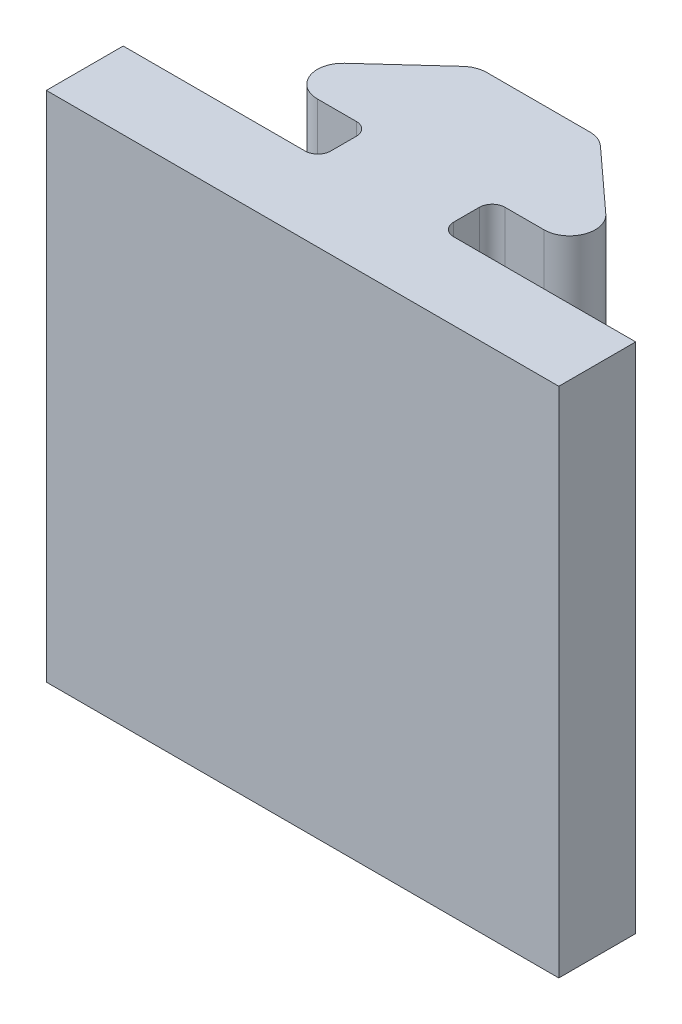
SolidWorks part; units mm, degrees
ref_plane "Front Plane" through (0, 0, 0) normal (0, 0, 1) x (1, 0, 0)
ref_plane "Top Plane" through (0, 0, 0) normal (0, 1, 0) x (1, 0, 0)
ref_plane "Right Plane" through (0, 0, 0) normal (1, 0, 0) x (0, 0, -1)
sketch "Sketch1" plane through (0, 0, 0) normal (0, 1, 0) x (1, 0, 0)
  line L0 (0, 0) -> (0, 4.5818) construction
  line L1 (-2.4, 4.5818) -> (2.4, 4.5818)
  line L2 (2.4, 4.5818) -> (7, 0.3818)
  line L3 (7, 0.3818) -> (2.4, 0.3818)
  line L4 (2.4, 0.3818) -> (2.4, -1.6182)
  line L5 (2.4, -1.6182) -> (10, -1.6182)
  line L6 (10, -1.6182) -> (10, -4.6182)
  line L7 (10, -4.6182) -> (-10, -4.6182)
  line L8 (-10, -1.6182) -> (-10, -4.6182)
  line L9 (-2.4, -1.6182) -> (-10, -1.6182)
  line L10 (-2.4, 0.3818) -> (-2.4, -1.6182)
  line L11 (-7, 0.3818) -> (-2.4, 0.3818)
  line L12 (-2.4, 4.5818) -> (-7, 0.3818)
  point P11 (0, -4.6182)
  dimension "D1" = 2.4
  dimension "D2" = 6.2
  dimension "D3" = 7
  dimension "D4" = 2
  dimension "D5" = 10
  dimension "D6" = 4.8
  dimension "D7" = 3
extrude "Boss-Extrude1" add sketch "Sketch1" along normal blind 20
fillet "Fillet1" radius 1 4 edges at (2.4, 10, -4.5818) (-2.4, 10, -4.5818) (-7, 10, -0.3818) (7, 10, -0.3818)
fillet "Fillet2" radius 0.5 4 edges at (2.4, 10, 1.6182) (2.4, 10, -0.3818) (-2.4, 10, 1.6182) (-2.4, 10, -0.3818)
